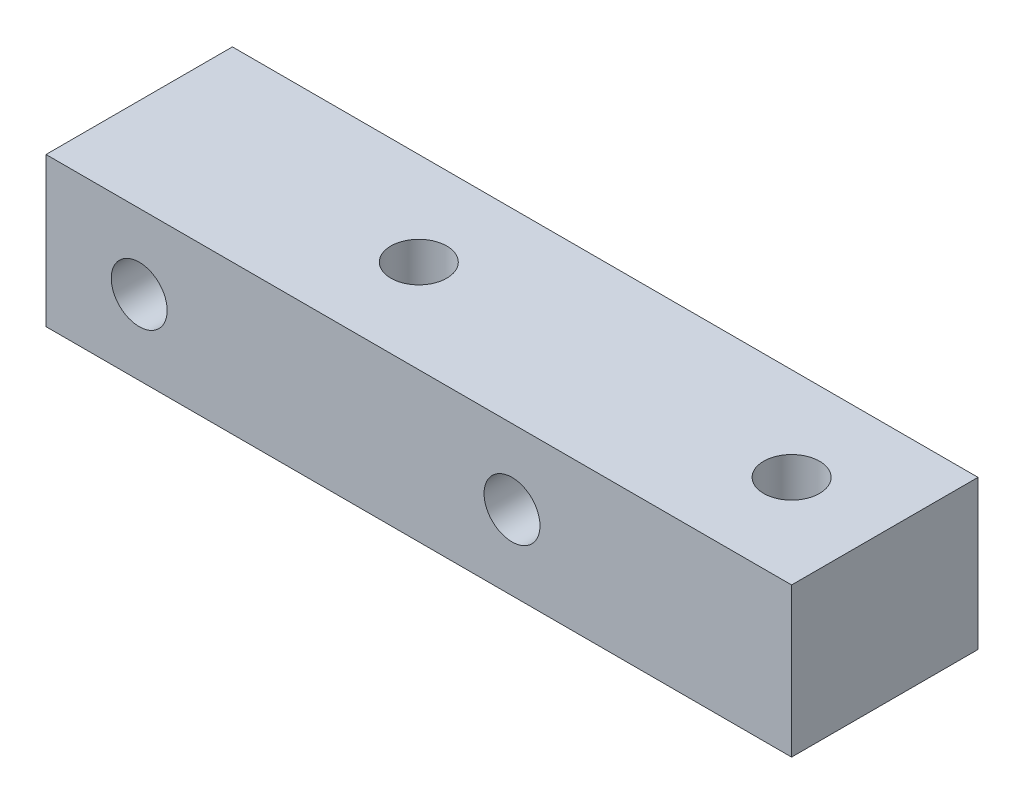
SolidWorks part; units mm, degrees
ref_plane "前视基准面" through (0, 0, 0) normal (0, 0, 1) x (1, 0, 0)
ref_plane "上视基准面" through (0, 0, 0) normal (0, 1, 0) x (1, 0, 0)
ref_plane "右视基准面" through (0, 0, 0) normal (1, 0, 0) x (0, 0, -1)
other "Configuration Table"
sketch "草图1" plane through (0, 0, 0) normal (0, 0, 1) x (1, 0, 0)
  line L0 (-20, 0) -> (20, 0) construction
  line L1 (-20, 4) -> (20, 4)
  line L2 (-20, 4) -> (-20, -4)
  line L3 (-20, -4) -> (20, -4)
  line L4 (20, 4) -> (20, -4)
  line L5 (-20, 4) -> (20, -4) construction
  line L6 (-20, -4) -> (20, 4) construction
  circle A0 centre (-15, 0) radius 1.5
  circle A2 centre (5, 0) radius 1.5
  point P0 (0, 0)
  dimension "D3" = 5
  dimension "D4" = 20
  dimension "D5" = 3
  dimension "D6" = 3
  dimension "D1" = 40
  dimension "D2" = 8
extrude "凸台-拉伸1" add sketch "草图1" along normal blind 10
sketch "草图2" plane through (0, 4, 0) normal (0, 1, 0) x (1, 0, 0)
  line L0 (-20, -5) -> (20, -5) construction
  line L1 (-20, -10) -> (-20, 0) construction
  line L2 (20, -10) -> (20, 0) construction
  circle A0 centre (15, -5) radius 1.5
  circle A1 centre (-5, -5) radius 1.5
  dimension "D1" = 5
  dimension "D3" = 3
  dimension "D4" = 3
  dimension "D2" = 20
extrude "切除-拉伸5" cut sketch "草图2" against normal through all contours A1 | A0
